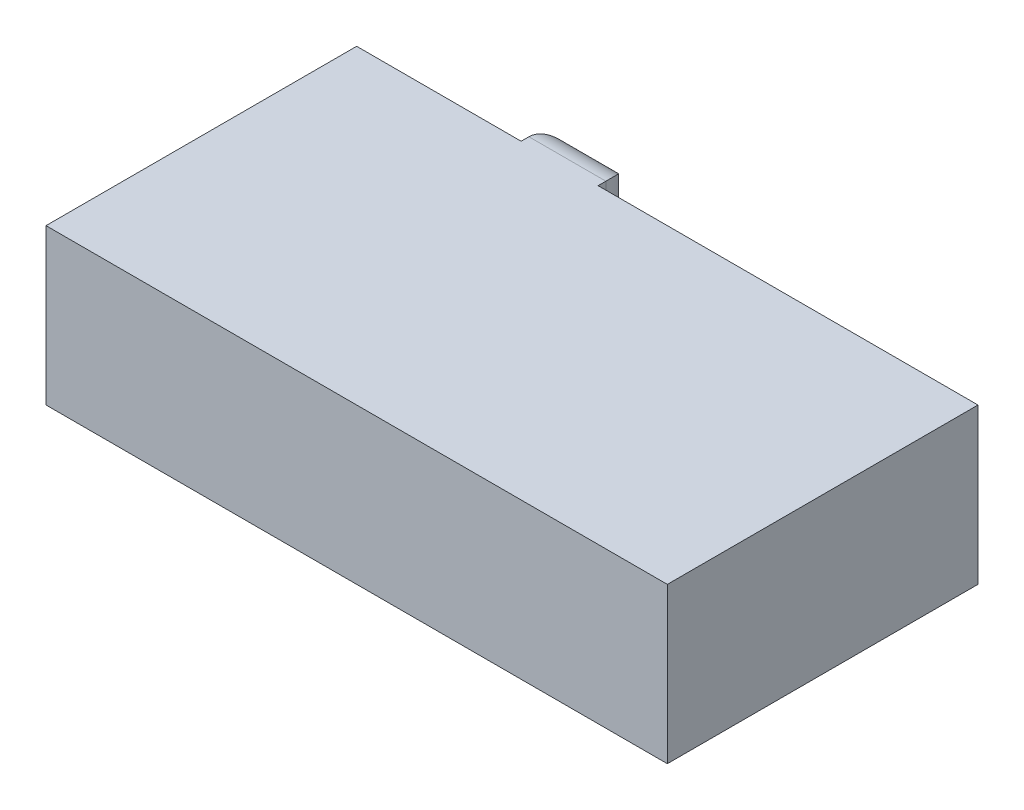
SolidWorks part; units mm, degrees
ref_plane "Front Plane" through (0, 0, 0) normal (0, 0, 1) x (1, 0, 0)
ref_plane "Top Plane" through (0, 0, 0) normal (0, 1, 0) x (1, 0, 0)
ref_plane "Right Plane" through (0, 0, 0) normal (1, 0, 0) x (0, 0, -1)
sketch "Sketch1" plane through (0, 0, 0) normal (0, 1, 0) x (1, 0, 0)
  line L1 (0, 0) -> (20.32, 0)
  line L2 (0, 0) -> (0, 10.16)
  line L3 (0, 10.16) -> (20.32, 10.16)
  line L4 (20.32, 0) -> (20.32, 10.16)
  dimension "D1" = 10.16
  dimension "D2" = 20.32
extrude "Boss-Extrude1" add sketch "Sketch1" along normal blind 5.08
sketch "Sketch3" plane through (0, 0, -10.16) normal (0, 0, -1) x (-1, 0, 0)
  line L0 (0, 5.08) -> (-5.3793, 5.08)
  line L1 (-20.32, 5.08) -> (0, 5.08) construction
  line L2 (-20.32, 0) -> (0, 0) construction
  line L3 (-5.3793, 5.08) -> (-7.896, 5.08)
  line L4 (-5.3793, 5.08) -> (-5.3793, 0)
  line L5 (-5.3793, 0) -> (-7.896, 0)
  line L6 (-7.896, 5.08) -> (-7.896, 0)
extrude "Boss-Extrude2" add sketch "Sketch3" along normal blind 1.27 contours L4 L5 L6 L3
fillet "Fillet1" radius 1.016 4 edges at (6.6377, 5.08, -11.43) (7.896, 2.54, -11.43) (6.6377, 0, -11.43) (5.3793, 2.54, -11.43)
